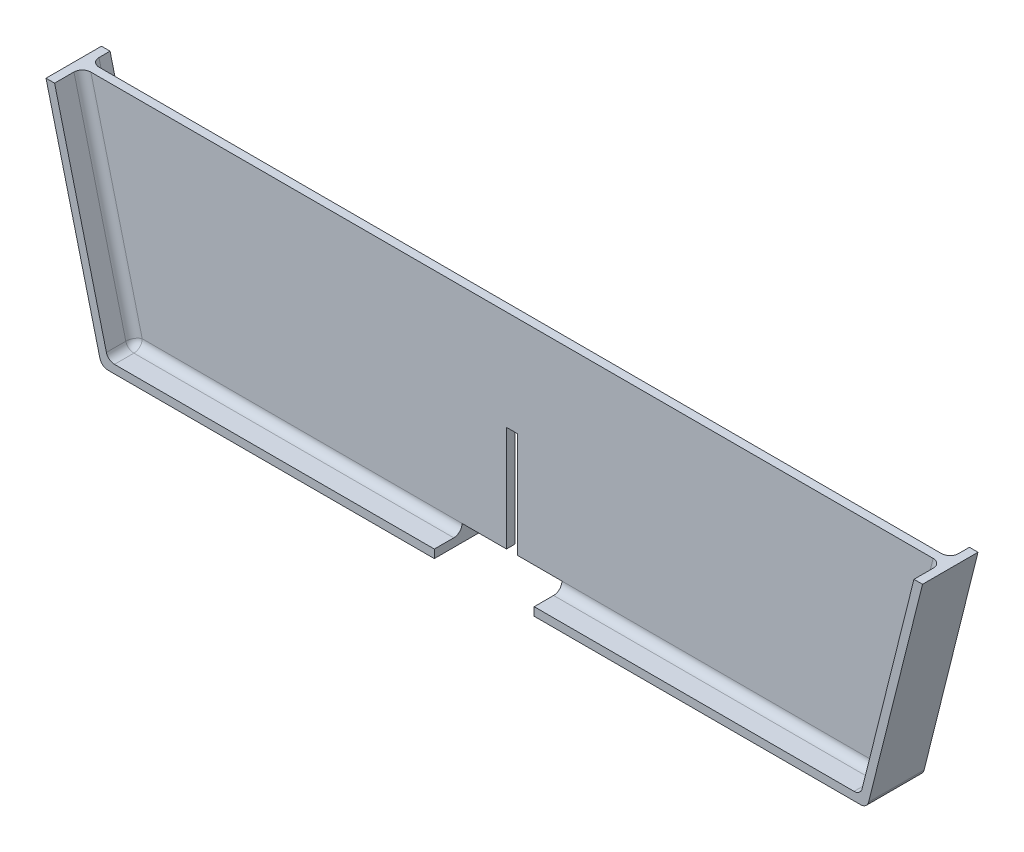
SolidWorks part; units mm, degrees
ref_plane "Front Plane" through (0, 0, 0) normal (0, 0, 1) x (1, 0, 0)
ref_plane "Top Plane" through (0, 0, 0) normal (0, 1, 0) x (1, 0, 0)
ref_plane "Right Plane" through (0, 0, 0) normal (1, 0, 0) x (0, 0, -1)
sketch "Sketch1" plane through (0, 0, 0) normal (0, 0, 1) x (1, 0, 0)
  line L0 (0, 0) -> (158, 0)
  line L1 (148, -40) -> (158, 0)
  line L2 (10, -40) -> (78, -40)
  line L3 (0, 0) -> (10, -40)
  line L9 (80, -40) -> (148, -40)
  line L11 (78, -40) -> (78, -18)
  line L12 (78, -18) -> (80, -18)
  line L13 (80, -40) -> (80, -18)
  point P4 (79, 0)
  point P5 (78, -40)
  dimension "D1" = 158
  dimension "D2" = 138
  dimension "D3" = 40
  dimension "D4" = 69
  dimension "D5" = 22
  dimension "D6" = 2
  dimension "D7" = 68
extrude "Boss-Extrude2" add sketch "Sketch1" along normal blind 1.5
sketch "Sketch5" plane through (0, 0, 1.5) normal (0, 0, 1) x (1, 0, 0)
  line L0 (146.8288, -38.5) -> (156.5448, 0.3638) construction
  line L1 (156.4538, 0) -> (158, 0)
  line L2 (88, -38.5) -> (88, -40)
  line L3 (70, -38.5) -> (70, -40)
  line L4 (78, -40) -> (78, -18) construction
  line L16 (148, -40) -> (158, 0) construction
  line L17 (80, -40) -> (148, -40) construction
  line L18 (10, -40) -> (78, -40) construction
  line L19 (0, 0) -> (10, -40) construction
  line L25 (148, -40) -> (158, 0)
  line L39 (88, -40) -> (148, -40)
  line L40 (10, -40) -> (70, -40)
  line L41 (0, 0) -> (10, -40)
  line L42 (1.5462, 0) -> (11.1712, -38.5)
  line L43 (11.1712, -38.5) -> (70, -38.5)
  line L44 (88, -38.5) -> (146.8288, -38.5)
  line L45 (146.8288, -38.5) -> (156.4538, 0)
  line L46 (1.4552, 0.3638) -> (11.1712, -38.5) construction
  line L47 (158, 0) -> (0, 0) construction
  line L48 (0, 0) -> (1.5462, 0)
  dimension "D2" = 8
  dimension "D3" = 8
  dimension "D1" = 1.5
extrude "Boss-Extrude3" add sketch "Sketch5" along normal blind 5 and the other way blind 5
fillet "Fillet1" radius 1.5 14 edges at (10, -40, 1.5) (6.3587, -19.25, 0) (40.5856, -38.5, 0) (11.1712, -38.5, -1.75) (146.8288, -38.5, -1.75) (151.6413, -19.25, 0) (148, -40, 1.5) (151.6413, -19.25, 1.5) (146.8288, -38.5, 4) (117.4144, -38.5, 1.5) (11.1712, -38.5, 4) (6.3587, -19.25, 1.5) (40.5856, -38.5, 1.5) (117.4144, -38.5, 0)
sketch "Sketch6" plane through (0, 0, 1.5) normal (0, 0, 1) x (1, 0, 0)
  line L1 (78, -40) -> (70, -40)
  line L2 (78, -40) -> (78, -37)
  line L3 (78, -37) -> (70, -37)
  line L4 (70, -40) -> (70, -37)
  line L5 (80, -40) -> (88, -40)
  line L6 (80, -40) -> (80, -37)
  line L7 (80, -37) -> (88, -37)
  line L8 (88, -40) -> (88, -37)
extrude "Cut-Extrude1" cut sketch "Sketch6" against normal up to next and the other way through all
equation "\"bl1\"=90"
equation "\"bw1\"=70"
